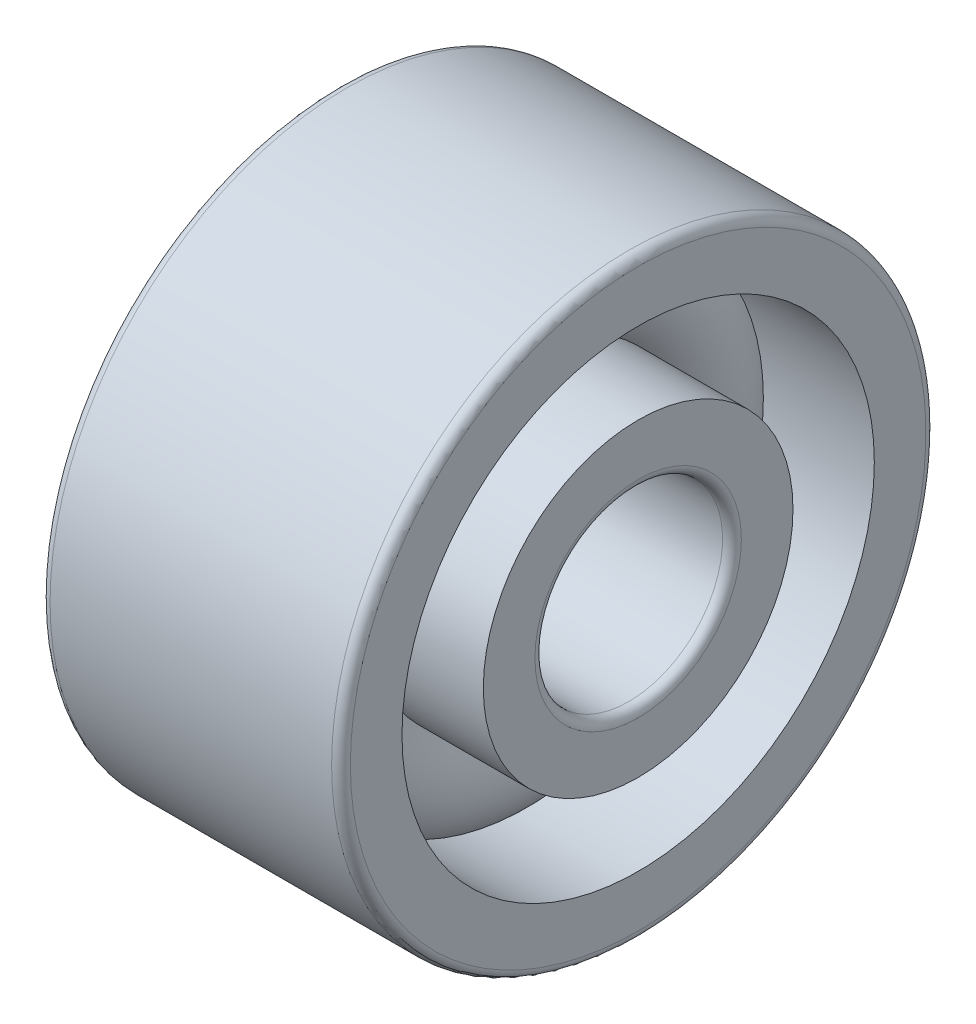
SolidWorks part; units mm, degrees
ref_plane "Front Plane" through (0, 0, 0) normal (0, 0, 1) x (1, 0, 0)
ref_plane "Top Plane" through (0, 0, 0) normal (0, 1, 0) x (1, 0, 0)
ref_plane "Right Plane" through (0, 0, 0) normal (1, 0, 0) x (0, 0, -1)
ref_plane "Plane1" through (0, 0, 0.1159) normal (0, 0, -1) x (-1, 0, 0)
sketch "Sketch1" plane through (0, 0, 0.1159) normal (0, 0, -1) x (-1, 0, 0)
  line L0 (-1.6076, 6.6292) -> (-6.3363, 6.6292)
  line L1 (-6.3363, 6.6292) -> (-6.3363, 4.4292)
  line L2 (-5.9363, 4.0292) -> (6.0637, 4.0292)
  line L3 (6.4637, 4.4292) -> (6.4637, 6.6292)
  line L4 (6.4637, 6.6292) -> (2.2683, 6.6292)
  line L5 (2.2683, 10.0959) -> (6.4637, 10.0959)
  line L6 (6.4637, 10.0959) -> (6.4637, 12.2959)
  line L7 (6.0637, 12.6959) -> (-5.9363, 12.6959)
  line L8 (-6.3363, 12.2959) -> (-6.3363, 10.0959)
  line L9 (-6.3363, 10.0959) -> (-1.6076, 10.0959)
  line L10 (-6.3363, 0.0292) -> (6.997, 0.0292) construction
  arc A0 (-6.3363, 4.4292) -> (-5.9363, 4.0292) centre (-5.9363, 4.4292) ccw
  arc A1 (6.0637, 4.0292) -> (6.4637, 4.4292) centre (6.0637, 4.4292) ccw
  arc A2 (2.2683, 6.6292) -> (2.2683, 10.0959) centre (0.3303, 8.3625) ccw
  arc A3 (6.4637, 12.2959) -> (6.0637, 12.6959) centre (6.0637, 12.2959) ccw
  arc A4 (-5.9363, 12.6959) -> (-6.3363, 12.2959) centre (-5.9363, 12.2959) ccw
  arc A5 (-1.6076, 10.0959) -> (-1.6076, 6.6292) centre (0.3303, 8.3625) ccw
  dimension "D1" = 4
  dimension "D2" = 12
revolve "Revolve1" add sketch "Sketch1" angle 360 about L10
